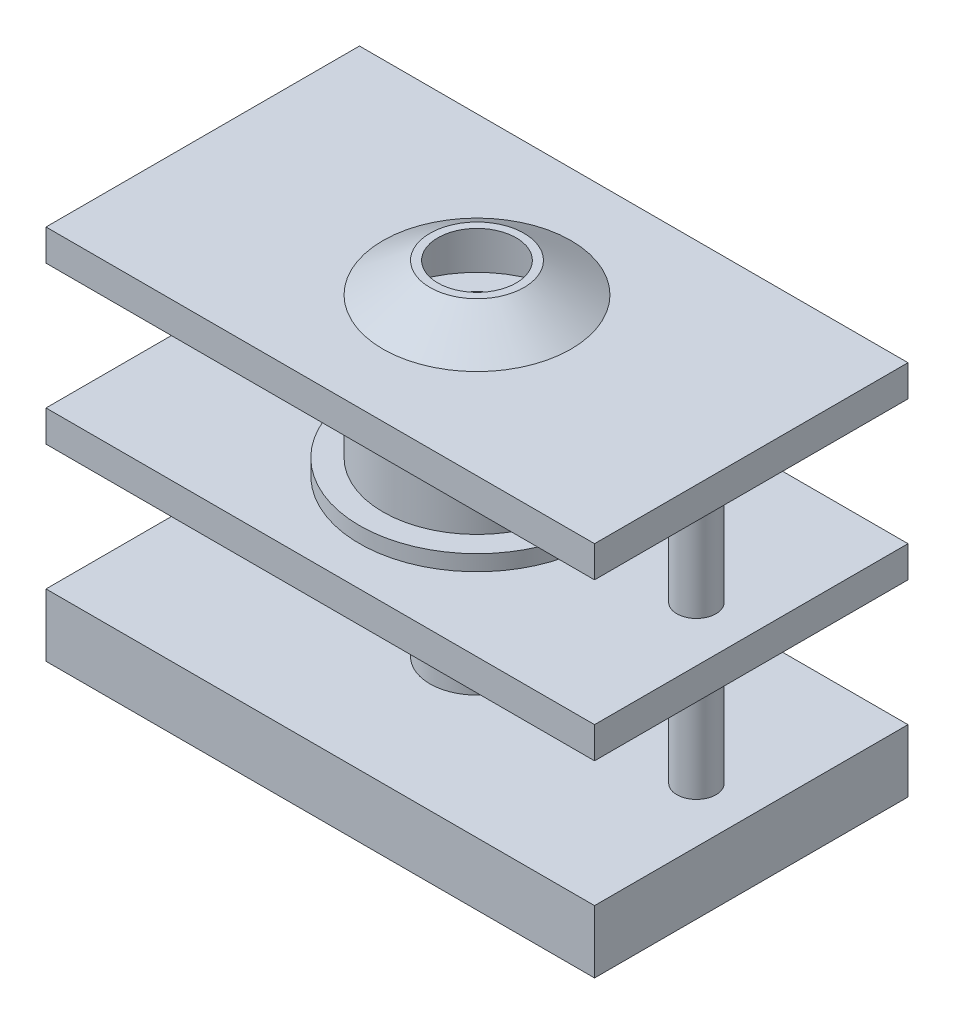
SolidWorks part; units mm, degrees
ref_plane "Front Plane" through (0, 0, 0) normal (0, 0, 1) x (1, 0, 0)
ref_plane "Top Plane" through (0, 0, 0) normal (0, 1, 0) x (1, 0, 0)
ref_plane "Right Plane" through (0, 0, 0) normal (1, 0, 0) x (0, 0, -1)
sketch "Sketch1" plane through (0, 0, 0) normal (0, 1, 0) x (1, 0, 0)
  line L1 (-350, -200) -> (350, -200)
  line L2 (-350, -200) -> (-350, 200)
  line L3 (-350, 200) -> (350, 200)
  line L4 (350, -200) -> (350, 200)
  line L5 (-350, -200) -> (350, 200) construction
  line L6 (-350, 200) -> (350, -200) construction
  circle A0 centre (-280, 0) radius 25
  circle A1 centre (280, 0) radius 25
  circle A5 centre (0, 0) radius 60
  point P0 (0, 0)
  dimension "D3" = 50
  dimension "D4" = 50
  dimension "D7" = 120
  dimension "D1" = 700
  dimension "D2" = 400
  dimension "D5" = 280
  dimension "D6" = 280
extrude "Boss-Extrude1" add sketch "Sketch1" along normal mid plane 80
ref_plane "Plane1" through (0, 200, 0) normal (0, 1, 0) x (1, 0, 0)
ref_plane "Plane2" through (0, 400, 0) normal (0, 1, 0) x (1, 0, 0)
sketch "Sketch4" plane through (0, 400, 0) normal (0, 1, 0) x (1, 0, 0)
  line L1 (-350, -200) -> (350, -200)
  line L2 (-350, -200) -> (-350, 200)
  line L3 (-350, 200) -> (350, 200)
  line L4 (350, -200) -> (350, 200)
  line L5 (-350, -200) -> (350, 200) construction
  line L6 (-350, 200) -> (350, -200) construction
  circle A2 centre (0, 0) radius 120
  point P0 (0, 0)
  dimension "D7" = 240
  dimension "D1" = 700
  dimension "D2" = 400
extrude "Boss-Extrude3" add sketch "Sketch4" along normal blind 40 separate body
sketch "Sketch5" plane through (0, 200, 0) normal (0, 1, 0) x (1, 0, 0)
  line L1 (-350, -200) -> (350, -200)
  line L2 (-350, -200) -> (-350, 200)
  line L3 (-350, 200) -> (350, 200)
  line L4 (350, -200) -> (350, 200)
  line L5 (-350, -200) -> (350, 200) construction
  line L6 (-350, 200) -> (350, -200) construction
  circle A0 centre (-280, 0) radius 25
  circle A1 centre (280, 0) radius 25
  circle A3 centre (0, 0) radius 60
  point P0 (0, 0)
  dimension "D3" = 50
  dimension "D4" = 50
  dimension "D7" = 120
  dimension "D1" = 700
  dimension "D2" = 400
  dimension "D5" = 280
  dimension "D6" = 280
extrude "Boss-Extrude5" add sketch "Sketch5" along normal blind 40 separate body
sketch "Sketch6" plane through (0, 40, 0) normal (0, 1, 0) x (1, 0, 0)
  circle A0 centre (0, 0) radius 60
  circle A1 centre (0, -5.1237) radius 50
  dimension "D1" = 120
  dimension "D2" = 100
extrude "Boss-Extrude6" add sketch "Sketch6" along normal blind 130
sketch "Sketch7" plane through (0, 40, 0) normal (0, 1, 0) x (1, 0, 0)
  circle A0 centre (-280, 0) radius 25
  circle A1 centre (280, 0) radius 25
  dimension "D1" = 50
  dimension "D2" = 50
extrude "Boss-Extrude7" add sketch "Sketch7" along normal blind 160 separate body
ref_plane "Plane3" through (0, 120, 0) normal (0, 1, 0) x (1, 0, 0)
sketch "Sketch8" plane through (0, 120, 0) normal (0, 1, 0) x (1, 0, 0)
  circle A0 centre (0, -5.1237) radius 50
  dimension "D1" = 100
extrude "Boss-Extrude8" add sketch "Sketch8" along normal blind 10
sketch "Sketch9" plane through (0, 130, 0) normal (0, 1, 0) x (1, 0, 0)
  circle A0 centre (0, 0) radius 5
  dimension "D1" = 10
extrude "Boss-Extrude9" add sketch "Sketch9" along normal blind 140
sketch "Sketch10" plane through (0, 170, 0) normal (0, 1, 0) x (1, 0, 0)
  circle A0 centre (0, 0) radius 60
  circle A1 centre (0, 1.4367) radius 90
  dimension "D1" = 120
  dimension "D2" = 180
extrude "Boss-Extrude10" add sketch "Sketch10" along normal blind 30
sketch "Sketch11" plane through (0, 270, 0) normal (0, 1, 0) x (1, 0, 0)
  circle A0 centre (0, 0) radius 90
  dimension "D1" = 180
extrude "Boss-Extrude11" add sketch "Sketch11" along normal blind 40
sketch "Sketch12" plane through (0, 240, 0) normal (0, 1, 0) x (1, 0, 0)
  circle A0 centre (0, 0) radius 150
  circle A1 centre (0, 0) radius 120
  dimension "D1" = 300
  dimension "D2" = 240
extrude "Boss-Extrude13" add sketch "Sketch12" along normal blind 20
sketch "Sketch13" plane through (0, 260, 0) normal (0, 1, 0) x (1, 0, 0)
  circle A0 centre (0, 0) radius 120
  circle A1 centre (0, 0) radius 90
  dimension "D1" = 240
  dimension "D2" = 180
extrude "Boss-Extrude15" add sketch "Sketch13" along normal blind 120
sketch "Sketch17" plane through (0, 400, 0) normal (0, -1, 0) x (1, 0, 0)
  circle A0 centre (0, 0) radius 150
  circle A1 centre (0, 0) radius 120
  dimension "D1" = 300
  dimension "D2" = 240
extrude "Boss-Extrude17" add sketch "Sketch17" along normal blind 20
sketch "Sketch18" plane through (0, 240, 0) normal (0, 1, 0) x (1, 0, 0)
  circle A0 centre (-280, 0) radius 25
  circle A1 centre (280, 0) radius 25
  dimension "D1" = 50
extrude "Boss-Extrude18" add sketch "Sketch18" along normal blind 160 separate body
sketch "Sketch20" plane through (0, 440, 0) normal (0, 1, 0) x (1, 0, 0)
  circle A0 centre (0, 0) radius 110
  dimension "D1" = 220
sketch "Sketch32" plane through (0, 0, 0) normal (0, 0, 1) x (1, 0, 0)
  line L0 (120, 440) -> (60, 478.0798)
  line L1 (110, 440) -> (50, 478.0798)
  line L2 (110, 440) -> (-110, 440) construction
  line L3 (50, 478.0798) -> (60, 478.0798)
  line L4 (110, 440) -> (120, 440)
  line L5 (0, 562.4639) -> (0, 377.1215) construction
  dimension "D1" = 50
  dimension "D2" = 60
revolve "Revolve1" add sketch "Sketch32" angle 360 about L5
